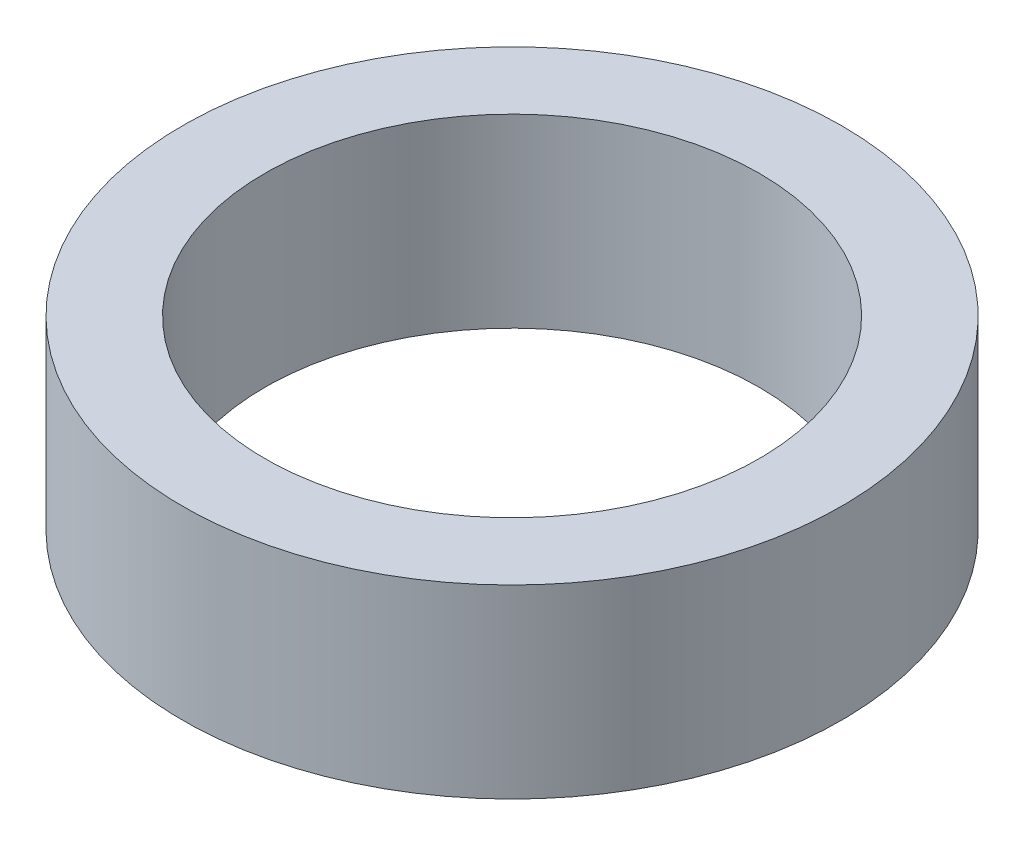
SolidWorks part; units mm, degrees
ref_plane "Alzado" through (0, 0, 0) normal (0, 0, 1) x (1, 0, 0)
ref_plane "Planta" through (0, 0, 0) normal (0, 1, 0) x (1, 0, 0)
ref_plane "Vista lateral" through (0, 0, 0) normal (1, 0, 0) x (0, 0, -1)
sketch "Sketch1" plane through (0, 0, 0) normal (0, 0, 1) x (1, 0, 0)
  line L0 (0.8, 0.45) -> (0.6, 0.45)
  line L1 (0.6, 0.45) -> (0.6, 0)
  line L2 (0.6, 0) -> (0.8, 0)
  line L3 (0.8, 0) -> (0.8, 0.45)
  line L4 (0, 0.45) -> (0, 0) construction
  dimension "D1" = 0.6
  dimension "D2" = 0.8
  dimension "D3" = 0.45
revolve "Revolve1" add sketch "Sketch1" angle 360 about L4
